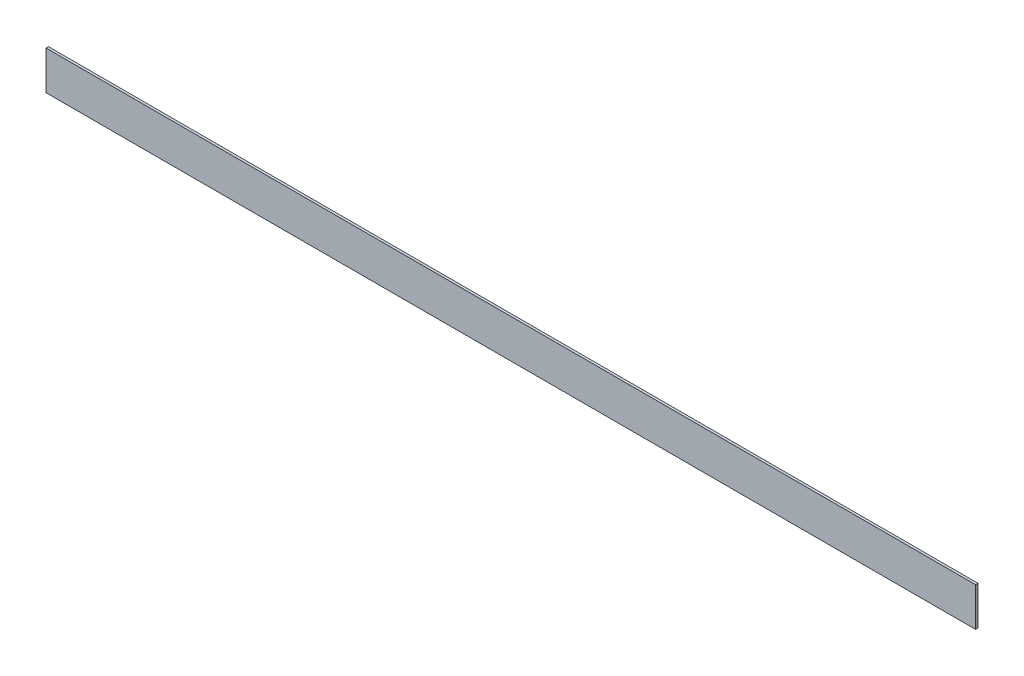
SolidWorks part; units mm, degrees
ref_plane "Front Plane" through (0, 0, 0) normal (0, 0, 1) x (1, 0, 0)
ref_plane "Top Plane" through (0, 0, 0) normal (0, 1, 0) x (1, 0, 0)
ref_plane "Right Plane" through (0, 0, 0) normal (1, 0, 0) x (0, 0, -1)
sketch "Sketch1" plane through (0, 0, 0) normal (0, 0, 1) x (1, 0, 0)
  line L1 (-304.8, 12.7) -> (304.8, 12.7)
  line L2 (-304.8, 12.7) -> (-304.8, -12.7)
  line L3 (-304.8, -12.7) -> (304.8, -12.7)
  line L4 (304.8, 12.7) -> (304.8, -12.7)
  line L5 (-304.8, 12.7) -> (304.8, -12.7) construction
  line L6 (-304.8, -12.7) -> (304.8, 12.7) construction
  point P0 (0, 0)
  dimension "D1" = 25.4
  dimension "D2" = 609.6
extrude "Boss-Extrude1" add sketch "Sketch1" along normal blind 1.5875
